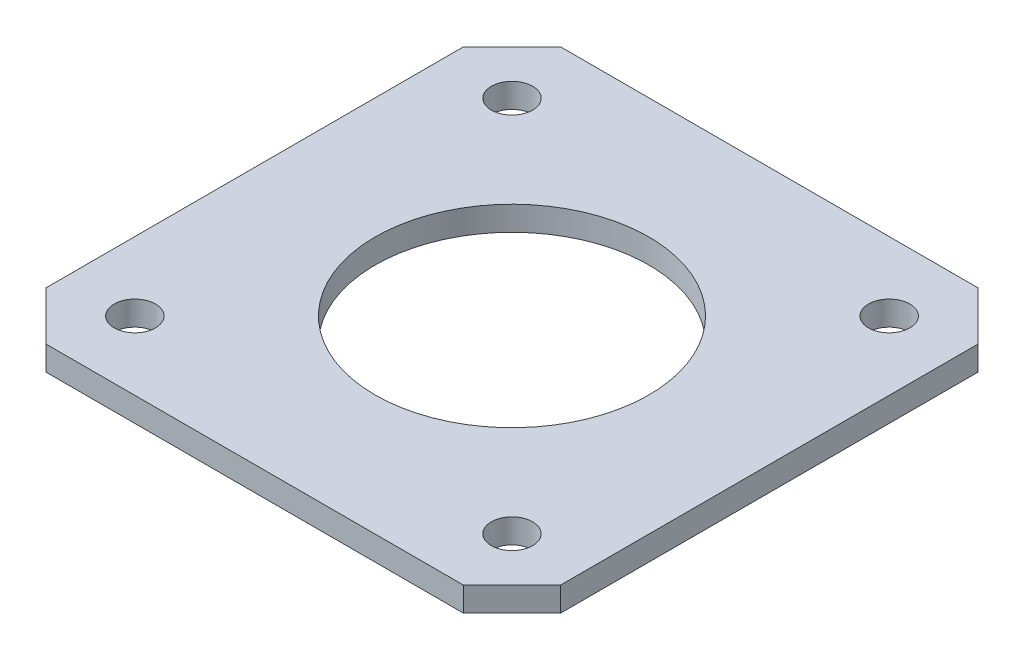
SolidWorks part; units mm, degrees
material "ONYX"
ref_plane "Front Plane" through (0, 0, 0) normal (0, 0, 1) x (1, 0, 0)
ref_plane "Top Plane" through (0, 0, 0) normal (0, 1, 0) x (1, 0, 0)
ref_plane "Right Plane" through (0, 0, 0) normal (1, 0, 0) x (0, 0, -1)
sketch "Sketch1" plane through (0, 0, 0) normal (0, 1, 0) x (1, 0, 0)
  line L1 (-21.15, 21.15) -> (21.15, 21.15)
  line L2 (-21.15, 21.15) -> (-21.15, -21.15)
  line L3 (-21.15, -21.15) -> (21.15, -21.15)
  line L4 (21.15, 21.15) -> (21.15, -21.15)
  line L5 (-21.15, 21.15) -> (21.15, -21.15) construction
  line L6 (-21.15, -21.15) -> (21.15, 21.15) construction
  point P0 (0, 0)
  dimension "D1" = 42.3
extrude "Boss-Extrude1" add sketch "Sketch1" along normal blind 2
sketch "Sketch2" plane through (0, 2, 0) normal (0, 1, 0) x (1, 0, 0)
  circle A0 centre (0, 0) radius 11.25
  dimension "D1" = 22.5
extrude "Cut-Extrude1" cut sketch "Sketch2" against normal through all
hole_wizard "M3 Clearance Hole1" positions "Sketch3" profile "Sketch4" hole size "M3" standard "ANSI Metric" end condition through all
sketch "Sketch3" plane through (0, 2, 0) normal (0, 1, 0) x (1, 0, 0)
  line L0 (0, 21.15) -> (0, -21.15) construction
  line L1 (21.15, 21.15) -> (-21.15, 21.15) construction
  line L2 (-21.15, -21.15) -> (21.15, -21.15) construction
  line L4 (-21.15, 0) -> (21.15, 0) construction
  line L5 (-21.15, 21.15) -> (-21.15, -21.15) construction
  line L6 (21.15, -21.15) -> (21.15, 21.15) construction
  point P0 (-15.5, 15.5)
  point P2 (15.5, 15.5)
  point P4 (15.5, -15.5)
  point P6 (-15.5, -15.5)
  point P24 (0, 0)
  dimension "D1" = 31
  dimension "D2" = 31
sketch "Sketch4" plane through (-15.5, 2, -15.5) normal (1, 0, 0) x (0, 0, 1)
  line L0 (0, 0) -> (0, 2)
  line L1 (0, 2) -> (1.7, 2)
  line L2 (1.7, 2) -> (1.7, 0)
  line L5 (1.7, 0) -> (0, 0)
  line L11 (0, -6.35) -> (0, 107.95) construction
  dimension "Thru Hole Dia." = 3.4
  dimension "Thru Hole Depth" = 2
chamfer "Chamfer1" distance 4 angle 45 4 edges at (21.15, 1, -21.15) (21.15, 1, 21.15) (-21.15, 1, 21.15) (-21.15, 1, -21.15)
